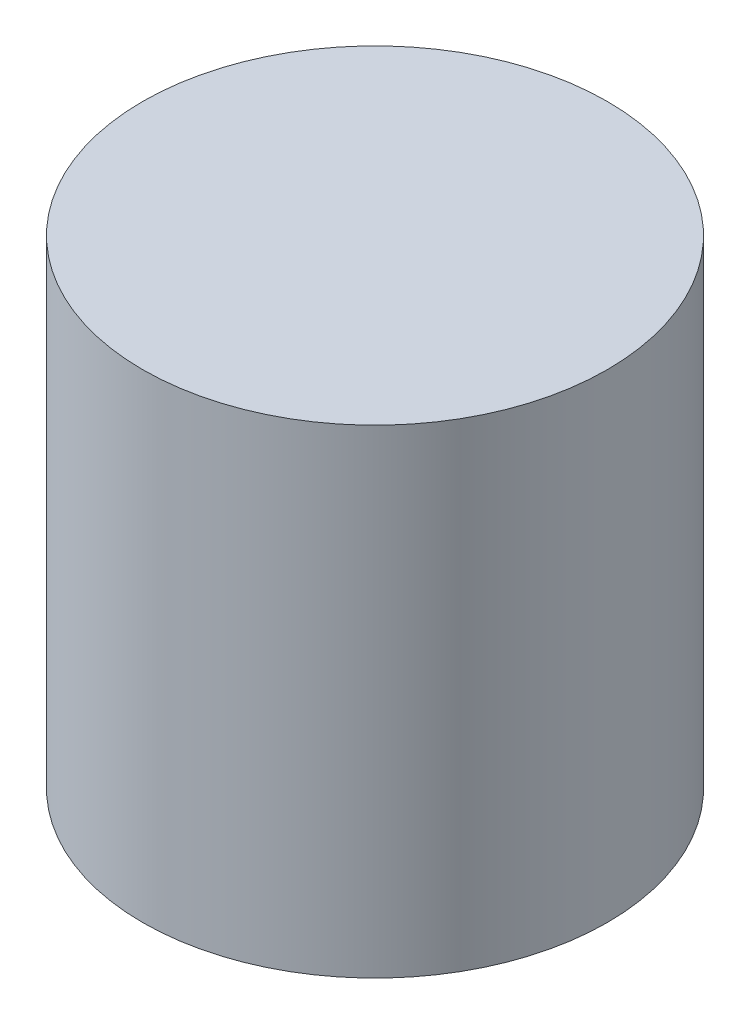
SolidWorks part; units mm, degrees
ref_plane "Front Plane" through (0, 0, 0) normal (0, 0, 1) x (1, 0, 0)
ref_plane "Top Plane" through (0, 0, 0) normal (0, 1, 0) x (1, 0, 0)
ref_plane "Right Plane" through (0, 0, 0) normal (1, 0, 0) x (0, 0, -1)
ref_plane "Plane1" through (0, -47.75, 0) normal (0, -1, 0) x (-1, 0, 0)
sketch "Sketch1" plane through (0, -47.75, 0) normal (0, -1, 0) x (-1, 0, 0)
  circle B0 centre (287.1745, 235) radius 49
sketch_block_instance "Block1-1"
sketch_block "Block1"
extrude "Boss-Extrude1" add sketch "Sketch1" against normal blind 101
